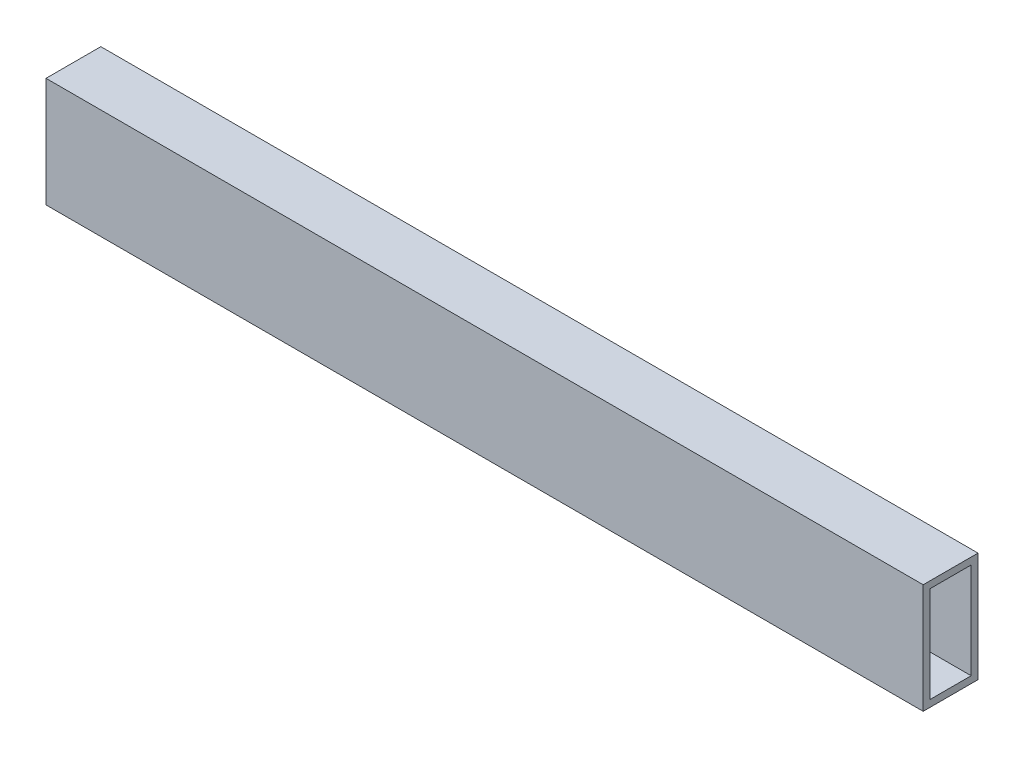
SolidWorks part; units mm, degrees
material "6061 Alloy"
ref_plane "Front Plane" through (0, 0, 0) normal (0, 0, 1) x (1, 0, 0)
ref_plane "Top Plane" through (0, 0, 0) normal (0, 1, 0) x (1, 0, 0)
ref_plane "Right Plane" through (0, 0, 0) normal (1, 0, 0) x (0, 0, -1)
sketch "Sketch1" plane through (0, 0, 0) normal (0, 1, 0) x (1, 0, 0)
  line L1 (-203.2, 12.7) -> (203.2, 12.7)
  line L2 (-203.2, 12.7) -> (-203.2, -12.7)
  line L3 (-203.2, -12.7) -> (203.2, -12.7)
  line L4 (203.2, 12.7) -> (203.2, -12.7)
  line L5 (-203.2, 12.7) -> (203.2, -12.7) construction
  line L6 (-203.2, -12.7) -> (203.2, 12.7) construction
  point P0 (0, 0)
  dimension "D1" = 406.4
  dimension "D2" = 25.4
extrude "Boss-Extrude1" add sketch "Sketch1" along normal mid plane 50.8
shell "Shell1" thickness 3.175
sketch "Sketch2" plane through (0, 25.4, 0) normal (0, 1, 0) x (1, 0, 0)
  line L0 (203.2, -12.7) -> (203.2, 12.7) construction
  circle A0 centre (190.5, 0) radius 3.175
  circle A8 centre (165.1, 0) radius 3.175
  circle A9 centre (139.7, 0) radius 3.175
  circle A10 centre (114.3, 0) radius 3.175
  circle A11 centre (88.9, 0) radius 3.175
  circle A12 centre (63.5, 0) radius 3.175
  circle A13 centre (38.1, 0) radius 3.175
  circle A14 centre (12.7, 0) radius 3.175
  circle A15 centre (-12.7, 0) radius 3.175
  circle A16 centre (-38.1, 0) radius 3.175
  circle A17 centre (-63.5, 0) radius 3.175
  circle A18 centre (-88.9, 0) radius 3.175
  circle A19 centre (-114.3, 0) radius 3.175
  circle A20 centre (-139.7, 0) radius 3.175
  circle A21 centre (-165.1, 0) radius 3.175
  circle A22 centre (-190.5, 0) radius 3.175
  circle A23 centre (-215.9, 0) radius 3.175
  circle A24 centre (-241.3, 0) radius 3.175
  circle A25 centre (-266.7, 0) radius 3.175
  circle A26 centre (-292.1, 0) radius 3.175
  dimension "D1" = 6.35
  dimension "D2" = 12.7
  dimension "D3" = 25.4
  dimension "D5" = 20
extrude "Cut-Extrude1" [suppressed] cut sketch "Sketch2" against normal through all
equation "\"A\"= 1"
equation "\"B\"= 2"
equation "\"C\"= 16"
equation "\"D1@Sketch1\"=\"C\""
equation "\"D2@Sketch1\"=\"A\""
equation "\"D1@Boss-Extrude1\"=\"B\""
equation "\"D\"= 1 / 8"
equation "\"D1@Shell1\"=\"D\""
equation "\"E\"= .25"
equation "\"F\"= 1 / 2"
equation "\"G\"= 1"
equation "\"D1@Sketch2\"=\"E\""
equation "\"D2@Sketch2\"=\"F\""
equation "\"D3@Sketch2\"=\"G\""
